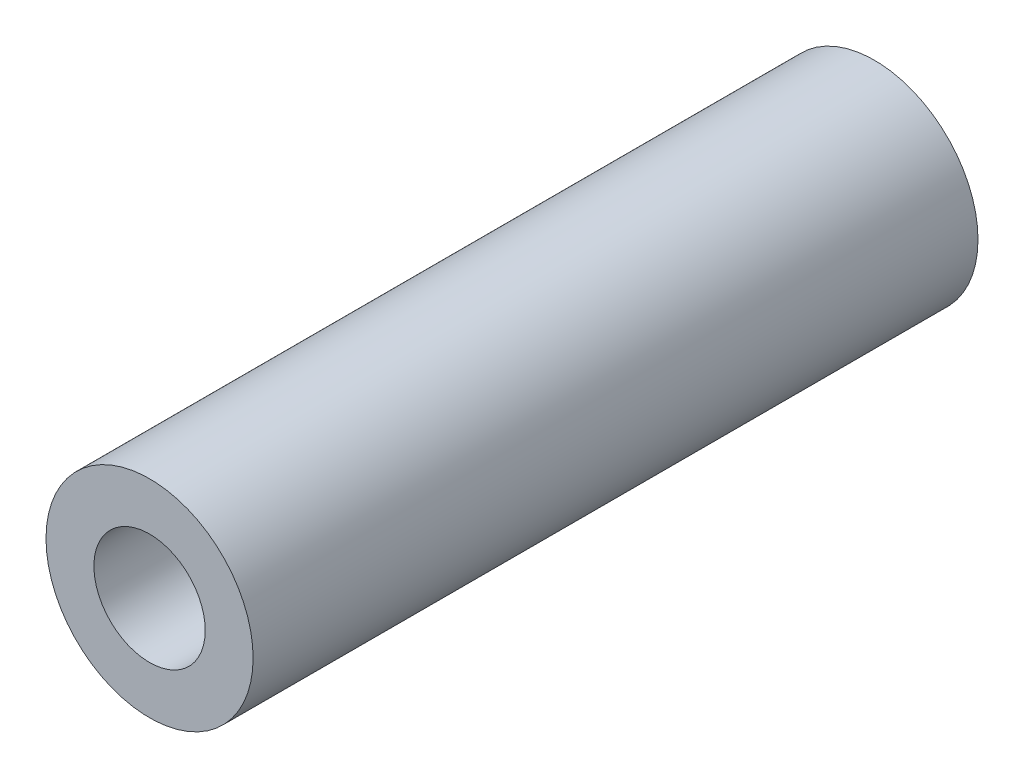
SolidWorks part; units mm, degrees
ref_plane "Front Plane" through (0, 0, 0) normal (0, 0, 1) x (1, 0, 0)
ref_plane "Top Plane" through (0, 0, 0) normal (0, 1, 0) x (1, 0, 0)
ref_plane "Right Plane" through (0, 0, 0) normal (1, 0, 0) x (0, 0, -1)
sketch "Sketch1" plane through (0, 0, 0) normal (0, 0, 1) x (1, 0, 0)
  circle A0 centre (0, 0) radius 2.15
  circle A1 centre (0, 0) radius 4
  dimension "D1" = 4.3
  dimension "D2" = 8
extrude "Boss-Extrude1" add sketch "Sketch1" along normal blind 28
